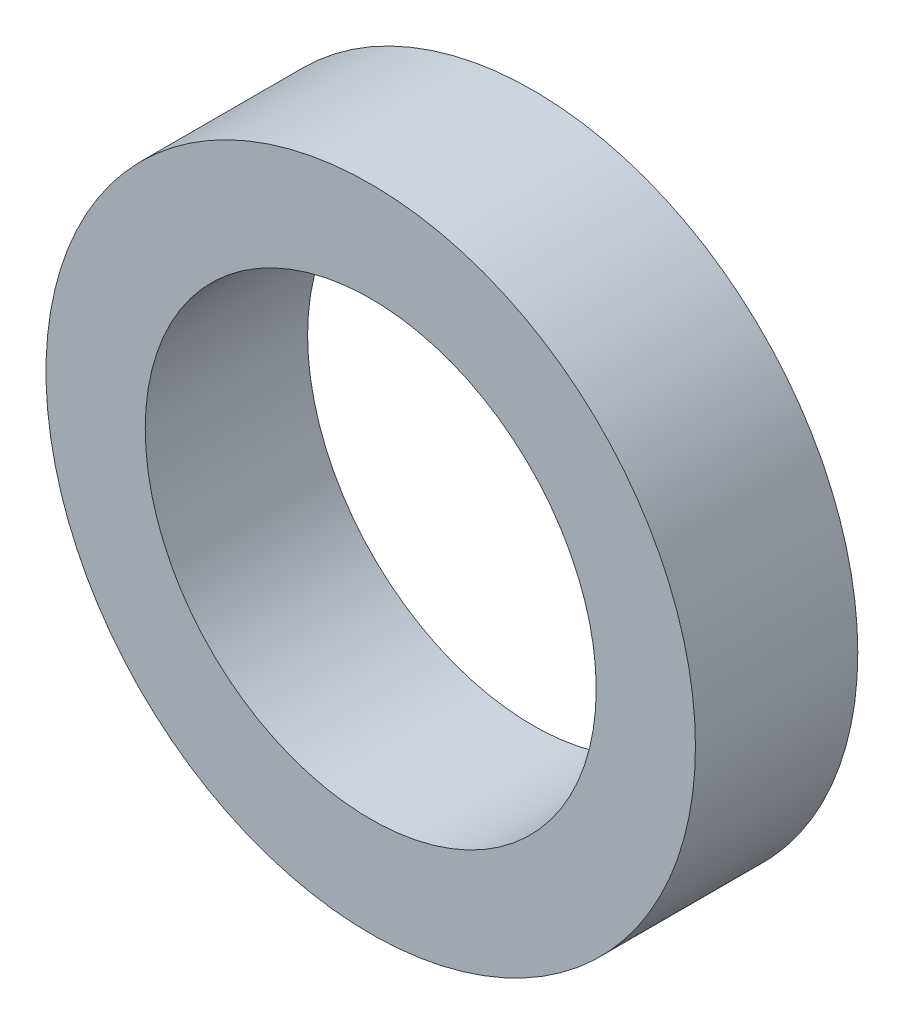
SolidWorks part; units mm, degrees
material "A3钢"
ref_plane "前视基准面" through (0, 0, 0) normal (0, 0, 1) x (1, 0, 0)
ref_plane "上视基准面" through (0, 0, 0) normal (0, 1, 0) x (1, 0, 0)
ref_plane "右视基准面" through (0, 0, 0) normal (1, 0, 0) x (0, 0, -1)
sketch "草图1" plane through (0, 0, 0) normal (0, 0, 1) x (1, 0, 0)
  circle A0 centre (0, 0) radius 9
  circle A1 centre (0, 0) radius 6.25
  dimension "D1" = 12.5
  dimension "D2" = 18
extrude "凸台-拉伸1" add sketch "草图1" along normal blind 4.5
